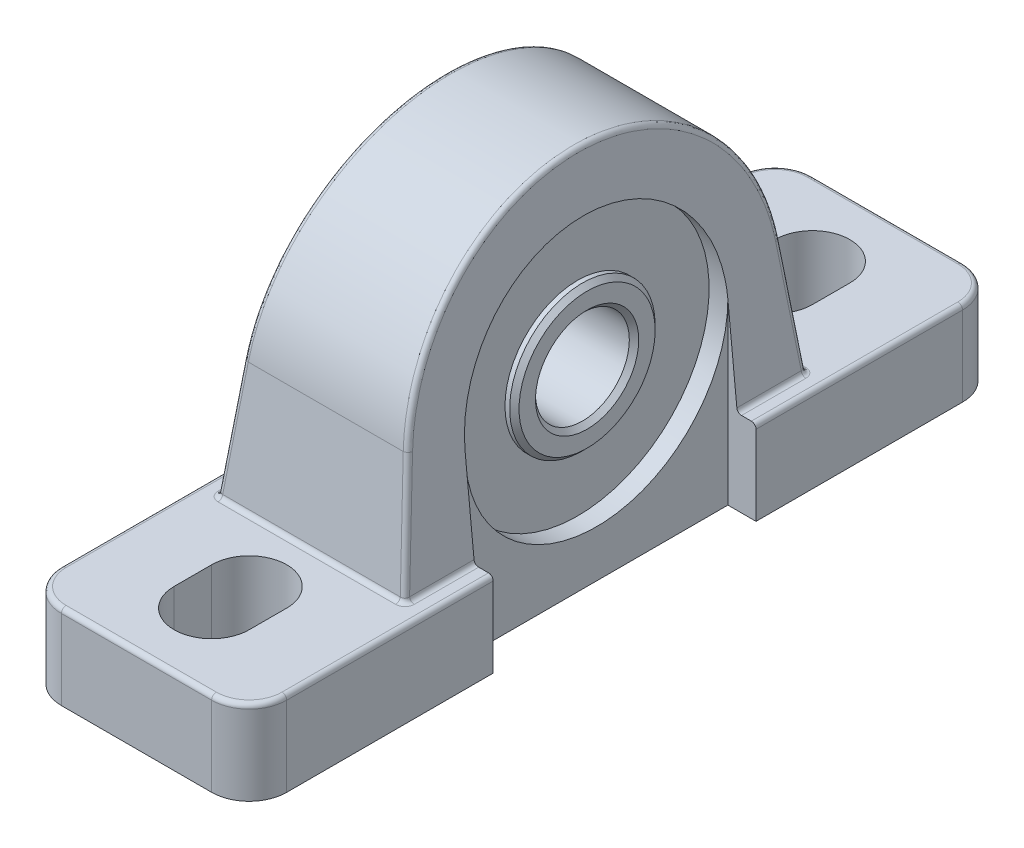
SolidWorks part; units mm, degrees
ref_plane "Alzado" through (0, 0, 0) normal (0, 0, 1) x (1, 0, 0)
ref_plane "Planta" through (0, 0, 0) normal (0, 1, 0) x (1, 0, 0)
ref_plane "Vista lateral" through (0, 0, 0) normal (1, 0, 0) x (0, 0, -1)
sketch "Sketch1" plane through (0, 0, 0) normal (0, 1, 0) x (1, 0, 0)
  line L1 (-19.05, 63.5) -> (19.05, 63.5)
  line L2 (-19.05, 63.5) -> (-19.05, -63.5)
  line L3 (-19.05, -63.5) -> (19.05, -63.5)
  line L4 (19.05, 63.5) -> (19.05, -63.5)
  line L5 (-19.05, 63.5) -> (19.05, -63.5) construction
  line L6 (-19.05, -63.5) -> (19.05, 63.5) construction
  point P0 (0, 0)
  dimension "D1" = 127
  dimension "D2" = 38.1
extrude "Boss-Extrude1" add sketch "Sketch1" along normal blind 14.2875
sketch "Sketch2" plane through (0, 0, 0) normal (0, 0, 1) x (1, 0, 0)
  line L0 (-15.875, 14.2875) -> (-11.1125, 61.9125)
  line L1 (-11.1125, 61.9125) -> (11.1125, 61.9125)
  line L2 (11.1125, 61.9125) -> (15.875, 14.2875)
  line L3 (15.875, 14.2875) -> (-15.875, 14.2875)
  line L4 (-19.05, 14.2875) -> (19.05, 14.2875) construction
  line L5 (19.05, 14.2875) -> (19.05, 0) construction
  line L6 (-19.05, 14.2875) -> (-19.05, 0) construction
  point P3 (0, 61.9125)
  dimension "D1" = 61.9125
  dimension "D2" = 22.225
  dimension "D3" = 3.175
  dimension "D4" = 3.175
extrude "Boss-Extrude2" add sketch "Sketch2" along normal mid plane 68
sketch "Sketch3" plane through (0, 0, 0) normal (1, 0, 0) x (0, 0, -1)
  line L0 (-34, 61.9125) -> (34, 61.9125) construction
  line L1 (-34, 14.2875) -> (-31.5012, 34.1296)
  line L2 (34, 14.2875) -> (31.5012, 34.1296)
  line L3 (34, 14.2875) -> (34, 65.0875)
  line L4 (34, 65.0875) -> (-34, 65.0875)
  line L5 (-34, 14.2875) -> (-34, 65.0875)
  arc A0 (31.5012, 34.1296) -> (-31.5012, 34.1296) centre (0, 30.1625) ccw
  dimension "D1" = 30.1625
  dimension "D2" = 50.8
extrude "Cut-Extrude1" cut sketch "Sketch3" against normal mid plane 50.8
sketch "Sketch4" plane through (0, 0, 0) normal (0, 1, 0) x (1, 0, 0)
  line L1 (-19.05, 22.225) -> (-14.2875, 22.225)
  line L2 (-19.05, 22.225) -> (-19.05, -22.225)
  line L3 (-19.05, -22.225) -> (-14.2875, -22.225)
  line L4 (-14.2875, 22.225) -> (-14.2875, -22.225)
  line L6 (-19.05, -63.5) -> (19.05, -63.5) construction
  line L7 (-19.05, 63.5) -> (-19.05, -63.5) construction
  point P4 (-19.05, 0)
  dimension "D1" = 4.7625
  dimension "D2" = 41.275
extrude "Cut-Extrude2" cut sketch "Sketch4" along normal through all
sketch "Sketch6" plane through (-19.05, 0, 0) normal (-1, 0, 0) x (0, 0, 1)
  circle A0 centre (0, 30.1625) radius 22.225
  dimension "D1" = 44.45
extrude "Cut-Extrude4" cut sketch "Sketch6" against normal blind 6.35
sketch "Sketch7" plane through (0, 14.2875, 0) normal (0, 1, 0) x (1, 0, 0)
  line L0 (0, -44.45) -> (0, -50.8) construction
  line L1 (6.35, -44.45) -> (6.35, -50.8)
  line L2 (-6.35, -44.45) -> (-6.35, -50.8)
  line L3 (0, 0) -> (19.05, 0) construction
  line L4 (19.05, -63.5) -> (19.05, 63.5) construction
  line L5 (0, 44.45) -> (0, 50.8) construction
  line L6 (6.35, 44.45) -> (6.35, 50.8)
  line L7 (-6.35, 44.45) -> (-6.35, 50.8)
  arc A0 (6.35, -44.45) -> (-6.35, -44.45) centre (0, -44.45) ccw
  arc A1 (-6.35, -50.8) -> (6.35, -50.8) centre (0, -50.8) ccw
  arc A2 (6.35, 44.45) -> (-6.35, 44.45) centre (0, 44.45) cw
  arc A3 (-6.35, 50.8) -> (6.35, 50.8) centre (0, 50.8) cw
  point P2 (0, -47.625)
  point P14 (0, 47.625)
  dimension "D3" = 19.05
  dimension "D1" = 47.625
  dimension "D2" = 12.7
extrude "Cut-Extrude5" cut sketch "Sketch7" against normal through all
ref_plane "Plane1" through (12.7, 0, 0) normal (1, 0, 0) x (0, 0, -1)
sketch "Sketch8" plane through (12.7, 0, 0) normal (-1, 0, 0) x (0, 0, 1)
  circle A0 centre (0, 30.1625) radius 12.3031
  dimension "D1" = 24.6062
extrude "Boss-Extrude3" add sketch "Sketch8" along normal blind 31.0007
sketch "Sketch9" plane through (-18.3007, 0, 0) normal (-1, 0, 0) x (0, 0, 1)
  circle A0 centre (0, 30.1625) radius 7.9375
  dimension "D1" = 15.875
extrude "Cut-Extrude6" cut sketch "Sketch9" against normal through all
sketch "Sketch10" plane through (-12.7, 0, 0) normal (-1, 0, 0) x (0, 0, 1)
  circle A0 centre (0, 30.1625) radius 22.225
  circle A2 centre (0, 30.1625) radius 12.3031
  circle A5 centre (0, 30.1625) radius 22.225 construction
  circle A6 centre (0, 30.1625) radius 12.3031 construction
extrude "Cut-Extrude7" cut sketch "Sketch10" against normal blind 1.5875
mirror "Mirror2" about plane through (0, 0, 0) normal (1, 0, 0) of "Cut-Extrude7", "Cut-Extrude4", "Cut-Extrude2"
fillet "Fillet1" radius 6.35 4 edges at (19.05, 7.1437, -63.5) (-19.05, 7.1437, -63.5) (19.05, 7.1437, 63.5) (-19.05, 7.1437, 63.5)
fillet "Fillet3" radius 0.7937 10 edges at (-19.05, 14.2875, 39.6875) (-17.1901, 14.2875, 61.6401) (19.05, 14.2875, 39.6875) (17.1901, 14.2875, 61.6401) (-19.05, 14.2875, -39.6875) (-17.1901, 14.2875, -61.6401) (0, 14.2875, -63.5) (17.1901, 14.2875, -61.6401) (0, 14.2875, 63.5) (19.05, 14.2875, -39.6875)
chamfer "Chamfer2" distance 0.7937 angle 45 4 edges at (12.7, 30.1625, -7.9375) (12.7, 30.1625, 12.3031) (-18.3007, 30.1625, 12.3031) (-18.3007, 30.1625, 7.9375)
fillet "Fillet5" radius 0.7937 12 edges at (15.875, 14.2875, -28.1125) (-15.875, 14.2875, -28.1125) (15.875, 14.2875, 28.1125) (-15.875, 14.2875, 28.1125) (14.8829, 24.2086, -32.7506) (-14.8829, 24.2086, -32.7506) (0, 14.2875, -34) (14.8829, 24.2086, 32.7506) (0, 14.2875, 34) (-14.8829, 24.2086, 32.7506) (11.1125, 61.9125, 0) (-11.1125, 61.9125, 0)
